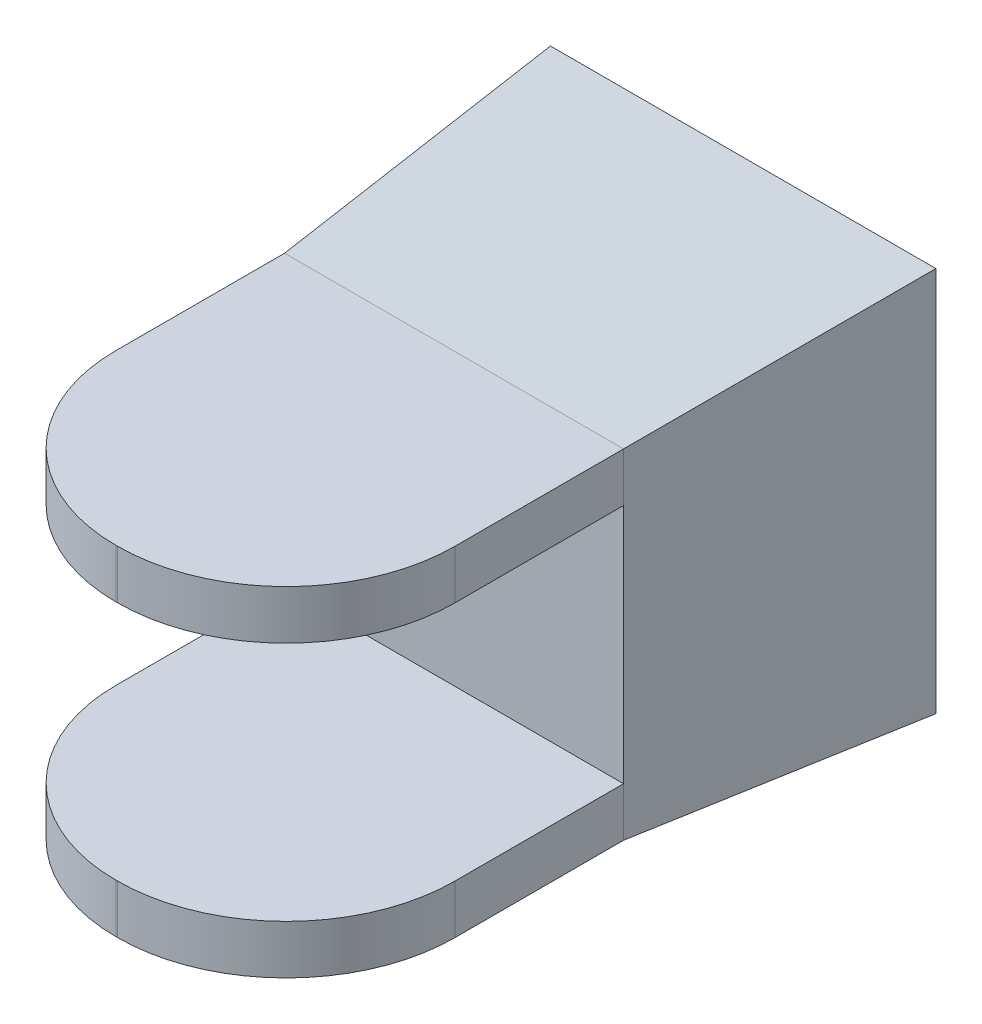
SolidWorks part; units mm, degrees
ref_plane "Płaszczyzna przednia" through (0, 0, 0) normal (0, 0, 1) x (1, 0, 0)
ref_plane "Płaszczyzna górna" through (0, 0, 0) normal (0, 1, 0) x (1, 0, 0)
ref_plane "Płaszczyzna prawa" through (0, 0, 0) normal (1, 0, 0) x (0, 0, -1)
sketch "Szkic1" plane through (0, 0, 0) normal (0, 0, 1) x (1, 0, 0)
  line L1 (-40, -40) -> (40, -40)
  line L2 (-40, -40) -> (-40, 40)
  line L3 (-40, 40) -> (40, 40)
  line L4 (40, -40) -> (40, 40)
  line L5 (-40, -40) -> (40, 40) construction
  line L6 (-40, 40) -> (40, -40) construction
  point P0 (0, 0)
  dimension "D1" = 80
  dimension "D2" = 80
extrude "Dodanie-wyciągnięcie1" add sketch "Szkic1" along normal blind 60 draft 4.6
sketch "Szkic6" plane through (0, 0, 60) normal (0, 0, 1) x (1, 0, 0)
  line L1 (-35.1725, -35.1725) -> (35.1725, -35.1725)
  line L2 (-35.1725, -35.1725) -> (-35.1725, 35.1725)
  line L3 (-35.1725, 35.1725) -> (35.1725, 35.1725)
  line L4 (35.1725, -35.1725) -> (35.1725, 35.1725)
extrude "Dodanie-wyciągnięcie2" add sketch "Szkic6" along normal blind 70
fillet "Zaokrąglenie3" radius 35 1 edges at (-35.1725, 0, 130)
fillet "Zaokrąglenie4" radius 35 1 edges at (35.1725, 0, 130)
sketch "Szkic7" plane through (0, 0, 130) normal (0, 0, 1) x (1, 0, 0)
  line L6 (-35.1725, 35.1725) -> (-35.1725, -35.1725) construction
  line L7 (35.1725, -25) -> (-35.1725, -25)
  line L8 (35.1725, -25) -> (35.1725, 25)
  line L9 (35.1725, 25) -> (-35.1725, 25)
  line L10 (-35.1725, -25) -> (-35.1725, 25)
  line L11 (35.1725, -25) -> (-35.1725, 25) construction
  line L12 (35.1725, 25) -> (-35.1725, -25) construction
  point P0 (0, 0)
extrude "Wytnij-wyciągnięcie3" cut sketch "Szkic7" against normal blind 70
sketch "Szkic8" plane through (0, -25, 0) normal (0, 1, 0) x (1, 0, 0)
  circle A0 centre (0, -94.7476) radius 35.3057
sketch "Szkic10" plane through (0, 0, 0) normal (0, 0, -1) x (-1, 0, 0)
  circle A2 centre (0, 0) radius 40
